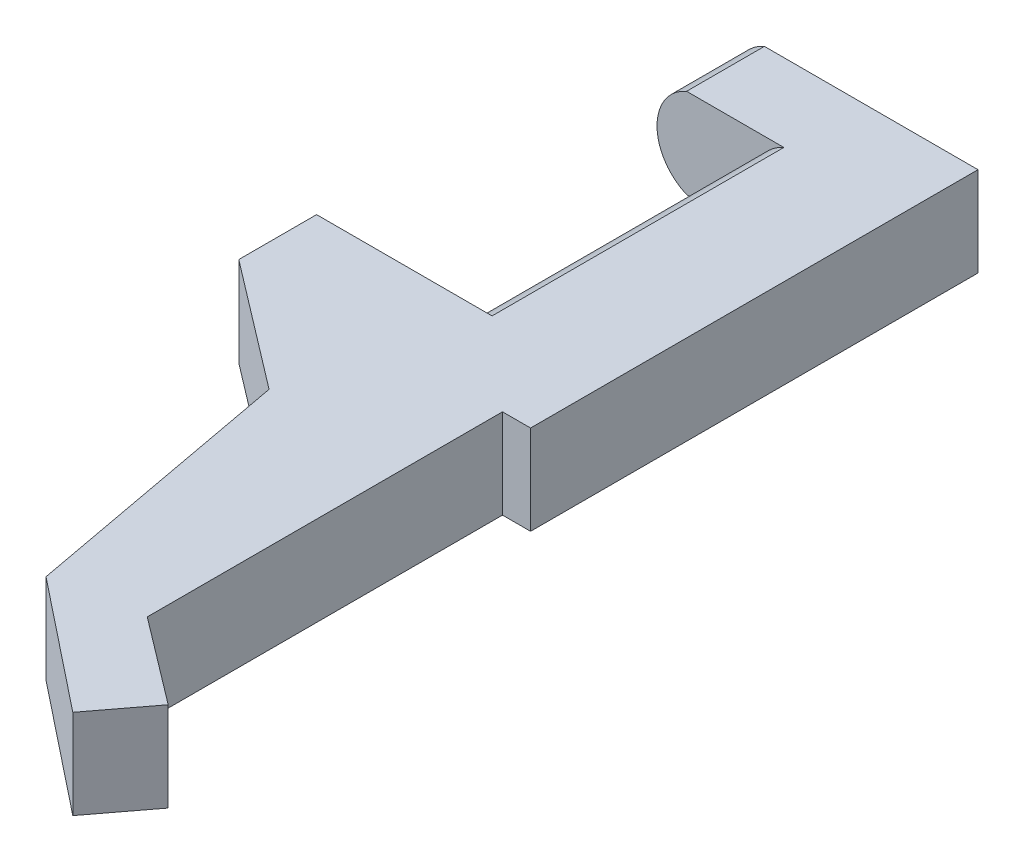
SolidWorks part; units mm, degrees
ref_plane "前视基准面" through (0, 0, 0) normal (0, 0, 1) x (1, 0, 0)
ref_plane "上视基准面" through (0, 0, 0) normal (0, 1, 0) x (1, 0, 0)
ref_plane "右视基准面" through (0, 0, 0) normal (1, 0, 0) x (0, 0, -1)
other "Configuration Table"
sketch "草图1" plane through (0, 0, 0) normal (0, 0, 1) x (1, 0, 0)
  line L0 (544.3012, 412.7441) -> (534.3012, 412.7441) construction
  line L1 (544.3012, 407.7441) -> (534.3012, 407.7441) construction
  line L2 (544.3012, 412.7441) -> (534.3012, 412.7441) construction
  line L3 (544.3012, 407.7441) -> (534.3012, 407.7441) construction
  line L4 (539.3012, 412.7441) -> (539.3012, 407.7441)
  line L5 (539.3012, 412.7441) -> (534.3012, 412.7441)
  line L6 (539.3012, 407.7441) -> (534.3012, 407.7441)
  arc A0 (534.3012, 412.7441) -> (534.3012, 407.7441) centre (534.3012, 410.2441) ccw construction
  arc A1 (534.3012, 412.7441) -> (534.3012, 407.7441) centre (534.3012, 410.2441) ccw
extrude "凸台-拉伸1" add sketch "草图1" against normal up to surface (15 mm away)
sketch "草图2" plane through (0, 0, -15) normal (0, 0, -1) x (-1, 0, 0)
  line L0 (-539.3012, 412.7441) -> (-529.3012, 412.7441)
  line L1 (-539.3012, 407.7441) -> (-529.3012, 407.7441)
  line L5 (-534.3012, 412.7441) -> (-539.3012, 412.7441)
  line L6 (-539.3012, 412.7441) -> (-539.3012, 407.7441)
  line L7 (-539.3012, 407.7441) -> (-534.3012, 407.7441)
  line L9 (-539.3012, 412.7441) -> (-539.3012, 407.7441)
  arc A0 (-534.3012, 407.7441) -> (-534.3012, 412.7441) centre (-534.3012, 410.2441) ccw construction
  arc A1 (-534.3012, 407.7441) -> (-534.3012, 412.7441) centre (-534.3012, 410.2441) ccw construction
  arc A2 (-529.3012, 407.7441) -> (-529.3012, 412.7441) centre (-529.3012, 410.2441) ccw
  arc A4 (-534.3012, 407.7441) -> (-534.3012, 412.7441) centre (-534.3012, 410.2441) ccw
  dimension "D1" = 0
extrude "凸台-拉伸2" add sketch "草图2" along normal blind 4
sketch "草图3" plane through (0, 0, 0) normal (0, 0, 1) x (1, 0, 0)
  line L0 (539.3012, 412.7441) -> (524.3012, 412.7441)
  line L1 (539.3012, 412.7441) -> (539.3012, 407.7441)
  line L2 (539.3012, 407.7441) -> (524.3012, 407.7441)
  line L3 (524.3012, 412.7441) -> (524.3012, 407.7441)
  dimension "D1" = 15
extrude "凸台-拉伸3" add sketch "草图3" along normal blind 4
ref_plane "基准面1" through (0, 410.2441, 0) normal (0, -1, 0) x (-1, 0, 0)
sketch "草图4" plane through (0, 410.2441, 0) normal (0, -1, 0) x (-1, 0, 0)
  line L0 (-524.3012, -4) -> (-539.3012, -4) construction
  line L1 (-524.3012, -4) -> (-537.8584, -4)
  line L2 (-534.3584, -4) -> (-534.3584, -24) construction
  line L3 (-534.3584, -24) -> (-540.9545, -29) construction
  line L4 (-537.8584, -22.2612) -> (-533.4673, -23.0751) construction
  line L5 (-537.8584, -4) -> (-537.8584, -22.2612)
  line L6 (-537.8584, -22.2612) -> (-542.3065, -25.633)
  line L9 (-524.3012, -4) -> (-530.8584, -9)
  line L10 (-542.3065, -25.633) -> (-540.1922, -28.4222)
  line L11 (-534.3584, -24) -> (-540.1922, -28.4222) construction
  line L12 (-530.8584, -9) -> (-533.4673, -23.0751)
  line L13 (-533.4673, -23.0751) -> (-540.1922, -28.4222)
  point P10 (-530.8584, -4)
  point P11 (-530.8584, -25.7388)
  point P12 (-538.0779, -31.2114)
  dimension "D1" = 20
  dimension "D2" = 5
  dimension "D5" = 5
  dimension "D3" = 3.5
extrude "凸台-拉伸4" add sketch "草图4" along normal mid plane 5
sketch "草图5" plane through (0, 0, -19) normal (0, 0, -1) x (-1, 0, 0)
  line L0 (-529.3012, 412.7441) -> (-539.3012, 412.7441) construction
  line L1 (-544.5488, 412.7441) -> (-522.4585, 412.7441)
  line L2 (-544.5488, 412.7441) -> (-544.5488, 412.5441)
  line L3 (-544.5488, 412.5441) -> (-522.4585, 412.5441)
  line L4 (-522.4585, 412.7441) -> (-522.4585, 412.5441)
  line L5 (-544.5488, 407.7441) -> (-522.4585, 407.7441)
  line L6 (-544.5488, 407.7441) -> (-544.5488, 407.9441)
  line L7 (-544.5488, 407.9441) -> (-522.4585, 407.9441)
  line L8 (-522.4585, 407.7441) -> (-522.4585, 407.9441)
  line L9 (-539.3012, 407.7441) -> (-529.3012, 407.7441) construction
  dimension "D1" = 0.2
  dimension "D2" = 0.2
extrude "切除-拉伸1" cut sketch "草图5" against normal through all
